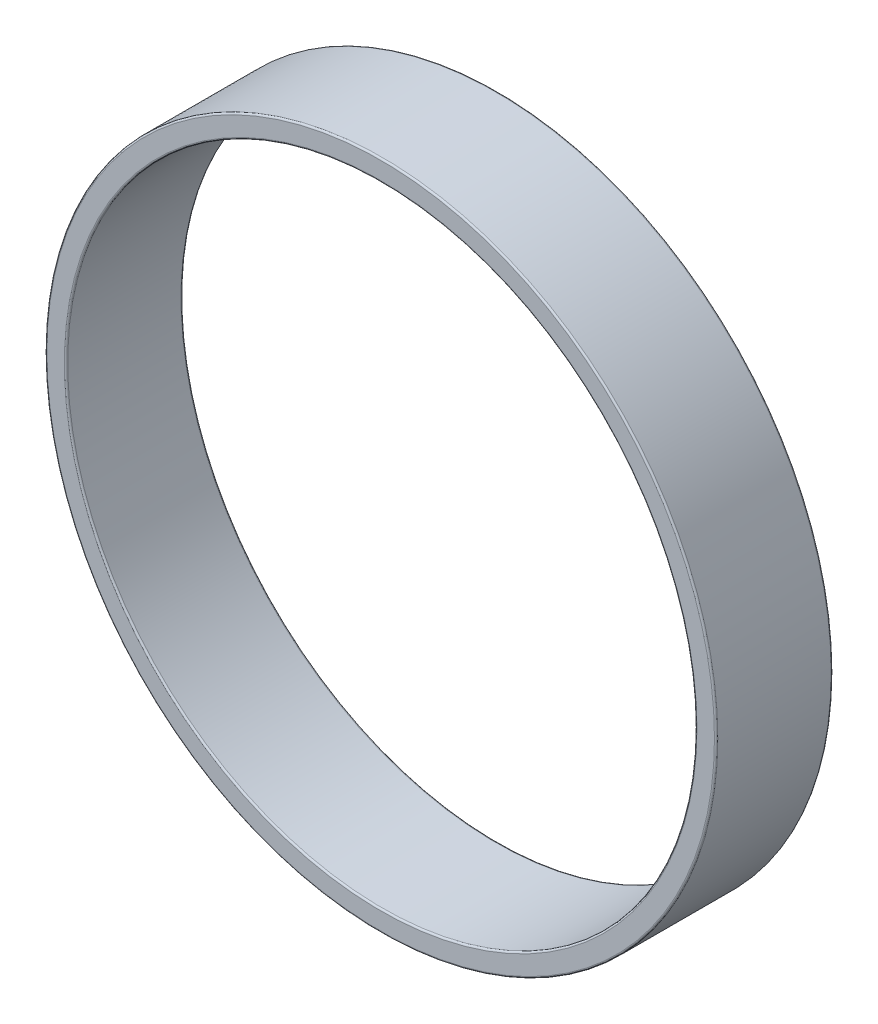
SolidWorks part; units mm, degrees
ref_plane "Front Plane" through (0, 0, 0) normal (0, 0, 1) x (1, 0, 0)
ref_plane "Top Plane" through (0, 0, 0) normal (0, 1, 0) x (1, 0, 0)
ref_plane "Right Plane" through (0, 0, 0) normal (1, 0, 0) x (0, 0, -1)
sketch "Sketch2" plane through (0, 0, 0) normal (0, 0, 1) x (1, 0, 0)
  circle A0 centre (0, 0) radius 75.5
  circle A1 centre (0, 0) radius 80.5
  dimension "D1" = 151
  dimension "D2" = 161
extrude "Boss-Extrude1" add sketch "Sketch2" along normal blind 28
fillet "Fillet1" radius 0.4 4 edges at (75.5, 0, 0) (75.5, 0, 28) (80.5, 0, 0) (80.5, 0, 28)
